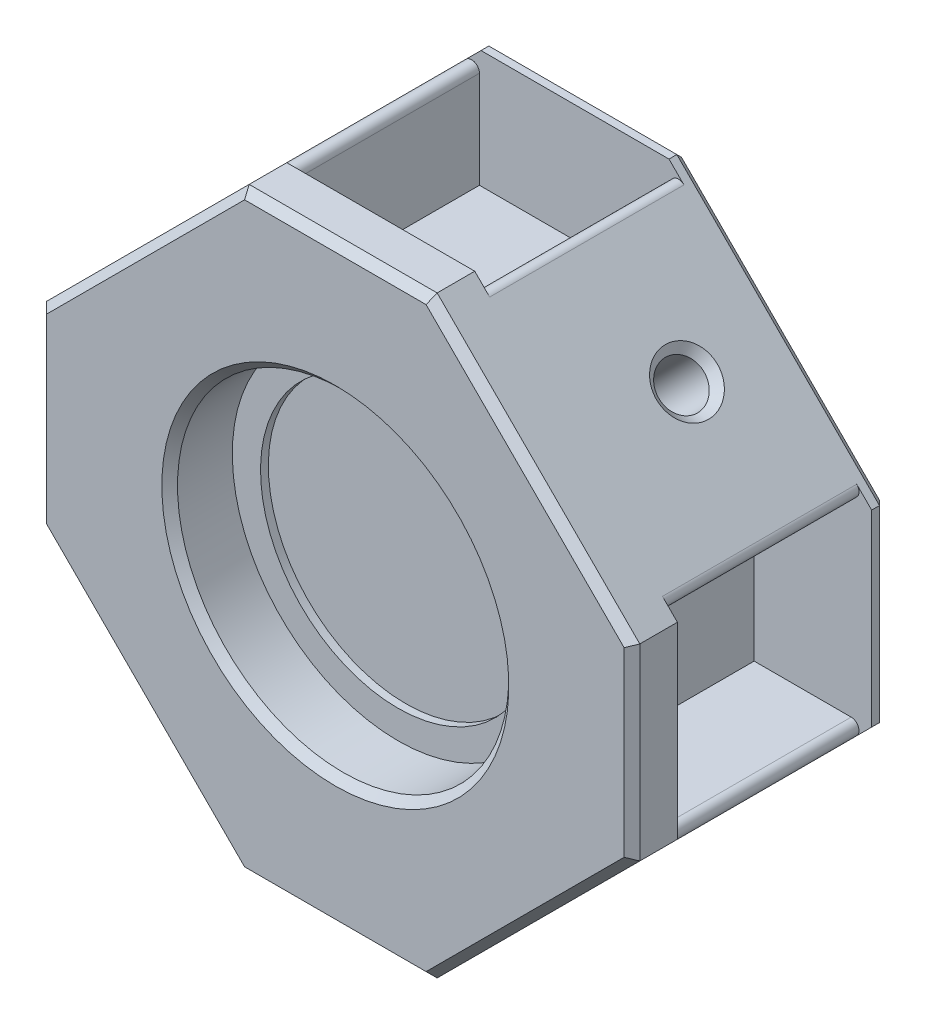
SolidWorks part; units mm, degrees
material "PLA"
ref_plane "Ebene vorne" through (0, 0, 0) normal (0, 0, 1) x (1, 0, 0)
ref_plane "Ebene oben" through (0, 0, 0) normal (0, 1, 0) x (1, 0, 0)
ref_plane "Ebene rechts" through (0, 0, 0) normal (1, 0, 0) x (0, 0, -1)
sketch "Skizze1" plane through (0, 0, 0) normal (0, 1, 0) x (1, 0, 0)
  line L0 (0, 0) -> (12, 0) construction
  line L1 (12, 0) -> (18.9367, 6.9367) construction
  line L2 (18.9367, 6.9367) -> (18.9367, 18.9367) construction
  line L3 (18.9367, 12.9367) -> (-12.2794, 12.9367) construction
  line L4 (12, 25.8734) -> (18.9367, 18.9367) construction
  line L5 (0, 25.8734) -> (12, 25.8734) construction
  line L6 (6, 0) -> (6, 25.8734) construction
  line L7 (0, 0) -> (-6.9367, 6.9367) construction
  line L8 (-6.9367, 6.9367) -> (-6.9367, 18.9367) construction
  line L9 (0, 25.8734) -> (-6.9367, 18.9367) construction
  line L10 (24.9367, 31.8734) -> (24.9367, -6)
  line L11 (24.9367, -6) -> (-12.9367, -6)
  line L12 (-12.9367, 31.8734) -> (-12.9367, -6)
  line L13 (24.9367, 31.8734) -> (-12.9367, 31.8734)
  point P18 (6, -6)
  point P19 (24.9367, 12.9367)
  point P20 (-12.9367, 12.9367)
  dimension "D1" = 12
  dimension "D2" = 135
  dimension "D3" = 9.81
  dimension "D4" = 12
  dimension "D5" = 6
  dimension "D6" = 6
extrude "Aufsatz-Linear austragen1" add sketch "Skizze1" along normal blind 20
sketch "Skizze2" plane through (0, 0, 0) normal (0, -1, 0) x (1, 0, 0)
  line L0 (6, 6) -> (6, -31.8734) construction
  line L3 (-12.9367, -12.9367) -> (24.9367, -12.9367) construction
  line L5 (24.9367, -31.8734) -> (-12.9367, -31.8734) construction
  line L6 (24.9367, 6) -> (24.9367, -31.8734) construction
  circle A0 centre (6, -12.9367) radius 10.575
  point P11 (6, -12.9367)
  dimension "D1" = 21.15
extrude "Schnitt-Linear austragen1" cut sketch "Skizze2" against normal blind 4
sketch "Skizze3" plane through (0, 0, 6) normal (0, 0, 1) x (1, 0, 0)
  line L0 (6, 0) -> (6, 20) construction
  line L3 (0, 3.2) -> (12, 3.2)
  line L4 (12, 3.2) -> (12, 15.2)
  line L5 (12, 15.2) -> (0, 15.2)
  line L6 (0, 3.2) -> (0, 15.2)
  line L7 (-12.9367, 0) -> (24.9367, 0) construction
  line L8 (-12.9367, 20) -> (24.9367, 20) construction
  point P11 (6, 15.2)
  point P12 (6, 3.2)
  dimension "D1" = 3.2
  dimension "D2" = 12
  dimension "D3" = 12
extrude "Schnitt-Linear austragen3" cut sketch "Skizze3" against normal blind 7.5 contours L5 L6 L3 L4
fillet "Verrundung1" radius 8 4 edges at (-12.9367, 10, -31.8734) (24.9367, 10, -31.8734) (24.9367, 10, 6) (-12.9367, 10, 6)
pattern_circular "Kreismuster1" count 4 over 360 about axis through (6, 0, -12.9367) along (0, 1, 0) of "Schnitt-Linear austragen3"
sketch "Skizze4" plane through (0, 4, 0) normal (0, -1, 0) x (1, 0, 0)
  circle A0 centre (6, -12.9367) radius 8.775
  circle A1 centre (6, -12.9367) radius 10.575 construction
  dimension "D1" = 1.8
extrude "Schnitt-Linear austragen4" cut sketch "Skizze4" against normal blind 0.5
move or copy body "Körper-Verschieben/Kopieren1" bodies to move or copy 106 copy no rotation origin (0, 10, -12.9367) rotation axis (-1, 0, 0) rotation angle 90
sketch "Skizze5" plane through (0, 0, -2.9367) normal (0, 0, 1) x (1, 0, 0)
  line L0 (0, 28.9367) -> (-12.9367, 16)
  line L1 (-4.9367, 28.9367) -> (16.9367, 28.9367) construction
  line L2 (-12.9367, 16) -> (-12.9367, 28.9367)
  line L3 (-12.9367, 28.9367) -> (0, 28.9367)
  line L4 (6, -8.9367) -> (6, 31.5737) construction
  line L5 (16.9367, -8.9367) -> (-4.9367, -8.9367) construction
  line L6 (24.9367, 10) -> (-21.788, 10) construction
  line L7 (24.9367, 20.9367) -> (24.9367, -0.9367) construction
  line L8 (24.9367, 16) -> (24.9367, 28.9367)
  line L9 (24.9367, 28.9367) -> (12, 28.9367)
  line L10 (12, 28.9367) -> (24.9367, 16)
  line L11 (12, -8.9367) -> (24.9367, 4)
  line L12 (24.9367, -8.9367) -> (12, -8.9367)
  line L13 (24.9367, 4) -> (24.9367, -8.9367)
  line L14 (-12.9367, -8.9367) -> (0, -8.9367)
  line L15 (-12.9367, 4) -> (-12.9367, -8.9367)
  line L16 (0, -8.9367) -> (-12.9367, 4)
extrude "Schnitt-Linear austragen5" cut sketch "Skizze5" against normal through all
sketch "Skizze6" plane through (-14.4684, 14.4684, 0) normal (-0.7071, 0.7071, 0) x (0.7071, 0.7071, 0)
  circle A0 centre (11.2842, 12.9367) radius 1.45
  point P2 (0, 0)
  dimension "D1" = 2.9
extrude "Schnitt-Linear austragen6" cut sketch "Skizze6" against normal blind 6 and the other way blind 10
pattern_circular "Kreismuster2" count 4 every 90 about axis through (6, 10, 0) along (0, 0, 1) of "Schnitt-Linear austragen6"
sketch "Skizze7" plane through (20.4684, 20.4684, 0) normal (0.7071, 0.7071, 0) x (0.7071, -0.7071, 0)
  line L4 (14.8045, 19.2367) -> (-20.8482, 19.2367)
  line L5 (14.8045, 22.9367) -> (14.8045, 18.1367) construction
  line L7 (-20.8482, 19.2367) -> (-20.8482, 28.5102)
  line L10 (-11.9761, 22.9367) -> (6.3192, 22.9367) construction
  line L11 (-12.6318, 18.2367) -> (8.0629, 18.2367) construction
  line L12 (-20.8482, 28.5102) -> (14.8045, 28.5102)
  line L13 (14.8045, 28.5102) -> (14.8045, 19.2367)
  dimension "D1" = 1
extrude "Schnitt-Linear austragen8" cut sketch "Skizze7" against normal through all
sketch "Skizze8" plane through (-12.9367, 0, 0) normal (-1, 0, 0) x (0, 0, 1)
  line L0 (-5.8367, 3.9) -> (-5.8367, 16.1)
  line L1 (-5.8367, 16.1) -> (-18.2367, 16.1)
  line L2 (-18.2367, 16.1) -> (-18.2367, 3.9)
  line L3 (-18.2367, 3.9) -> (-5.8367, 3.9)
  line L4 (-6.1367, 16) -> (-18.1367, 16) construction
  line L5 (-6.1367, 4) -> (-6.1367, 16) construction
  dimension "D1" = 12.2
  dimension "D2" = 0.1
  dimension "D3" = 0.3
  dimension "D4" = 12.4
extrude "Schnitt-Linear austragen9" cut sketch "Skizze8" against normal blind 7.5
pattern_circular "Kreismuster11" count 4 over 360 about axis through (6, 10, 0) along (0, 0, 1) of "Schnitt-Linear austragen9"
chamfer "Fase1" distance 0.5 angle 45 21 edges at (-6.4684, 22.4684, -2.9367) (6, 28.9367, -2.9367) (18.4684, 22.4684, -2.9367) (24.9367, 10, -2.9367) (18.4684, -2.4684, -2.9367) (6, -8.9367, -2.9367) (-6.4684, -2.4684, -2.9367) (-12.9367, 10, -2.9367) (6, -0.575, -2.9367) (17.4639, -3.4728, -12.9367) (-7.4728, -1.4639, -12.9367) (-5.4639, 23.4728, -12.9367) (19.4728, 21.4639, -12.9367) (24.9367, 10, -19.2367) (18.4684, 22.4684, -19.2367) (6, 28.9367, -19.2367) (-6.4684, 22.4684, -19.2367) (-12.9367, 10, -19.2367) (-6.4684, -2.4684, -19.2367) (6, -8.9367, -19.2367) (18.4684, -2.4684, -19.2367)
fillet "Verrundung2" radius 0.5 8 edges at (-0.1, 28.8367, -12.0367) (12.1, 28.8367, -12.0367) (24.8367, 16.1, -12.0367) (24.8367, 3.9, -12.0367) (12.1, -8.8367, -12.0367) (-0.1, -8.8367, -12.0367) (-12.8367, 16.1, -12.0367) (-12.8367, 3.9, -12.0367)
